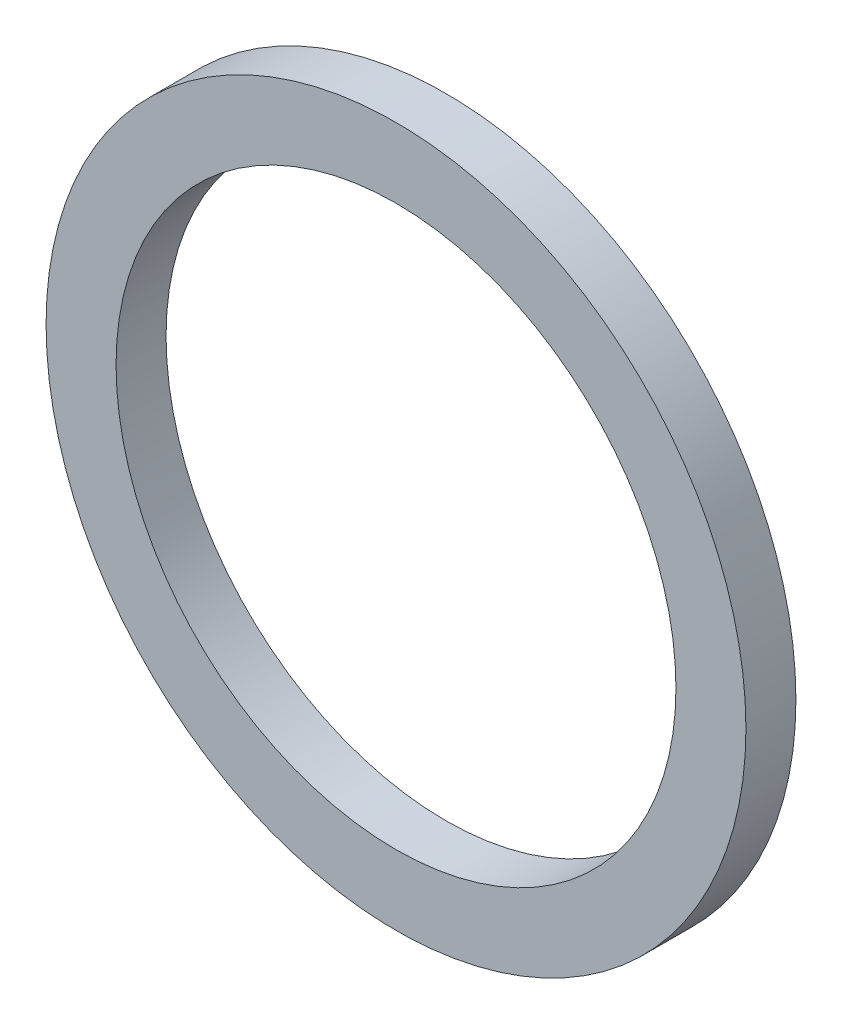
SolidWorks part; units mm, degrees
ref_plane "Front Plane" through (0, 0, 0) normal (0, 0, 1) x (1, 0, 0)
ref_plane "Top Plane" through (0, 0, 0) normal (0, 1, 0) x (1, 0, 0)
ref_plane "Right Plane" through (0, 0, 0) normal (1, 0, 0) x (0, 0, -1)
sketch "Sketch1" plane through (0, 0, 0) normal (0, 0, 1) x (1, 0, 0)
  circle A0 centre (0, 0) radius 7
  circle A1 centre (0, 0) radius 5.6
  dimension "D1" = 14
  dimension "D2" = 11.2
extrude "Boss-Extrude1" add sketch "Sketch1" along normal blind 1
